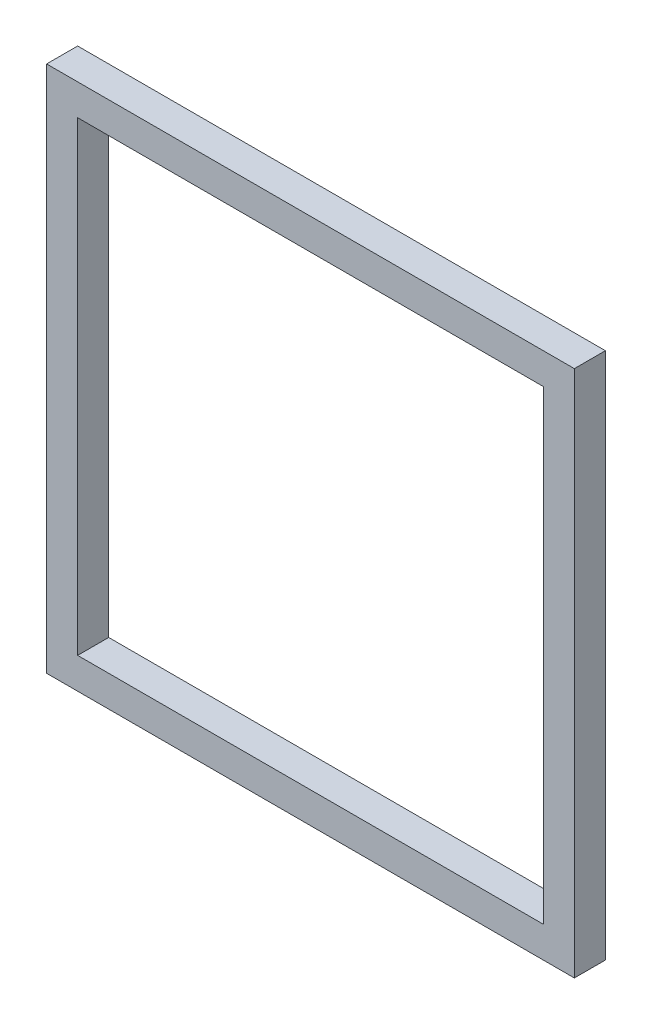
SolidWorks part; units mm, degrees
ref_plane "Front Plane" through (0, 0, 0) normal (0, 0, 1) x (1, 0, 0)
ref_plane "Top Plane" through (0, 0, 0) normal (0, 1, 0) x (1, 0, 0)
ref_plane "Right Plane" through (0, 0, 0) normal (1, 0, 0) x (0, 0, -1)
sketch "Sketch1" plane through (0, 0, 0) normal (0, 0, 1) x (1, 0, 0)
  line L0 (20, -20) -> (20, -320)
  line L1 (0, 0) -> (340, 0)
  line L2 (0, 0) -> (0, -340)
  line L3 (0, -340) -> (340, -340)
  line L4 (340, 0) -> (340, -340)
  line L5 (20, -320) -> (320, -320)
  line L6 (320, -320) -> (320, -20)
  line L7 (320, -20) -> (20, -20)
  point P9 (170, 0)
  dimension "D1" = 340
  dimension "D2" = 340
  dimension "D3" = 20
  dimension "D4" = 20
  dimension "D5" = 20
  dimension "D6" = 20
extrude "Boss-Extrude1" add sketch "Sketch1" along normal blind 20
